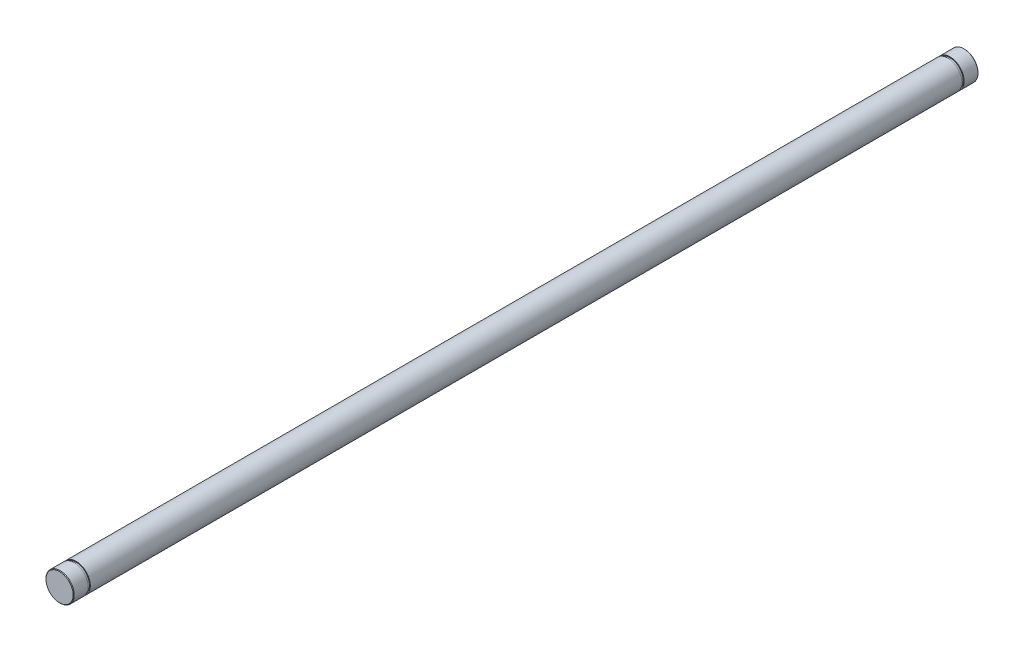
SolidWorks part; units mm, degrees
ref_plane "Front Plane" through (0, 0, 0) normal (0, 0, 1) x (1, 0, 0)
ref_plane "Top Plane" through (0, 0, 0) normal (0, 1, 0) x (1, 0, 0)
ref_plane "Right Plane" through (0, 0, 0) normal (1, 0, 0) x (0, 0, -1)
sketch "Sketch1" plane through (0, 0, 0) normal (0, 0, 1) x (1, 0, 0)
  circle A0 centre (0, 0) radius 4.7625 construction
  dimension "Diameter" = 9.525
sketch "Sketch2" plane through (0, 0, 0) normal (1, 0, 0) x (0, 0, -1)
  line L0 (152.4, 0) -> (-152.4, 0) construction
  point P0 (-121.92, 0)
  point P3 (0, 0)
  point P4 (121.92, 0)
  point P6 (-106.68, 0)
  point P7 (106.68, 0)
  dimension "Length" = 304.8
  dimension "D1" = 30.48
  dimension "D2" = 30.48
  dimension "D3" = 45.72
  dimension "D4" = 45.72
sketch "Sketch3" plane through (0, 0, 0) normal (0, 0, 1) x (1, 0, 0)
  circle A0 centre (0, 0) radius 4.7625 construction
  circle A1 centre (0, 0) radius 4.7625
extrude "Boss-Extrude1" add sketch "Sketch3" along normal up to vertex (152.4 mm away) and the other way up to vertex (152.4 mm away) up to point (0, 0, 152.4) other way up to point (0, 0, -152.4)
chamfer "Chamfer1" distance 0.1905 angle 45 2 edges at (4.7625, 0, 152.4) (4.7625, 0, -152.4)
sketch "Sketch4" plane through (0, 0, 0) normal (0, 1, 0) x (1, 0, 0)
  line L0 (4.7625, -152.2095) -> (4.7625, 152.2095) construction
  line L1 (4.7625, 147.5366) -> (4.4704, 147.5366)
  line L2 (4.7625, 147.5366) -> (4.7625, 146.8)
  line L3 (4.7625, 146.8) -> (4.4704, 146.8)
  line L4 (4.4704, 147.5366) -> (4.4704, 146.8)
  line L5 (0, -1000) -> (0, 49000) construction
  line L6 (0, 0) -> (4.7625, 0) construction
  line L7 (4.7625, -146.8) -> (4.4704, -146.8)
  line L8 (4.4704, -147.5366) -> (4.4704, -146.8)
  line L9 (4.7625, -147.5366) -> (4.4704, -147.5366)
  line L10 (4.7625, -147.5366) -> (4.7625, -146.8)
  line L12 (4.572, 152.4) -> (-4.572, 152.4) construction
  dimension "D1" = 8.9408
  dimension "D2" = 0.7366
  dimension "D3" = 5.6
revolve "Cut-Revolve1" cut sketch "Sketch4" angle 360 about L5
equation "\"D1@Chamfer1\"=\"Diameter@Sketch1\"*.02"
equation "\"D1@Sketch2\"=\"D2@Sketch2\""
equation "\"D2@Sketch2\"=\"Length@Sketch2\"*.1"
equation "\"D3@Sketch2\"=\"Length@Sketch2\"*.15"
equation "\"D4@Sketch2\"=\"D3@Sketch2\""
